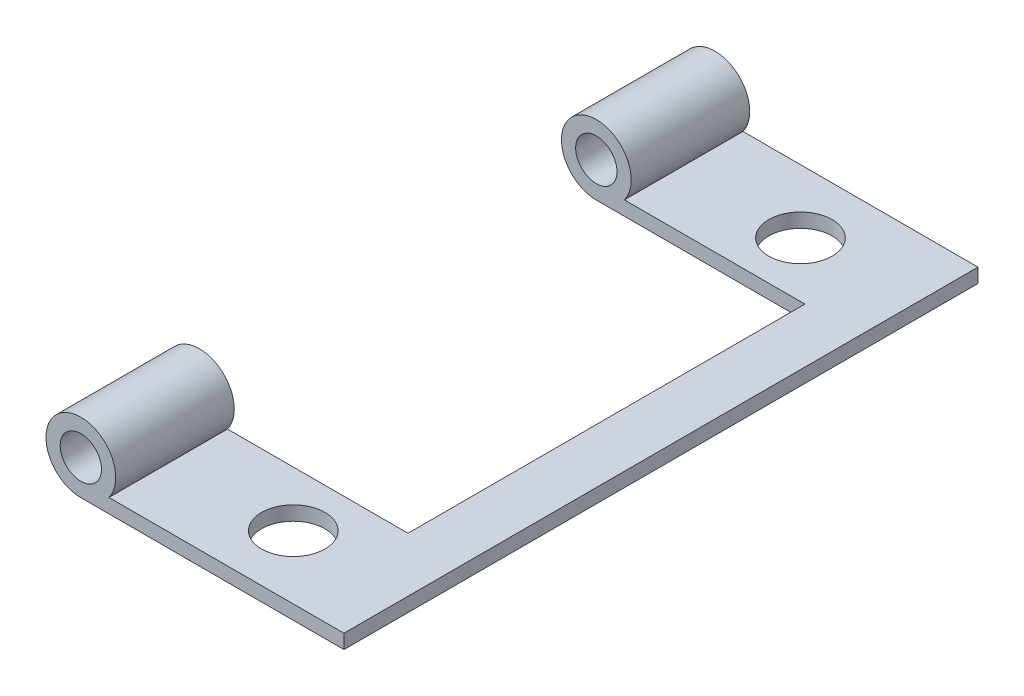
SolidWorks part; units mm, degrees
ref_plane "Front Plane" through (0, 0, 0) normal (0, 0, 1) x (1, 0, 0)
ref_plane "Top Plane" through (0, 0, 0) normal (0, 1, 0) x (1, 0, 0)
ref_plane "Right Plane" through (0, 0, 0) normal (1, 0, 0) x (0, 0, -1)
sketch "Sketch2" plane through (0, 0, 0) normal (0, 1, 0) x (1, 0, 0)
  line L0 (0, 25) -> (0, -25) construction
  line L1 (-9, 25) -> (9, 25)
  line L2 (-9, 25) -> (-9, 15.65)
  line L3 (-9, -25) -> (9, -25)
  line L4 (9, 25) -> (9, -25)
  line L5 (-9, 25) -> (9, -25) construction
  line L6 (-9, -25) -> (9, 25) construction
  line L7 (0, 22.5) -> (9, 22.5) construction
  line L8 (0, -22.5) -> (9, -22.5) construction
  line L9 (-9, -15.65) -> (-9, -25)
  line L10 (-9, 15.65) -> (4.7, 15.65)
  line L12 (-9, -15.65) -> (4.7, -15.65)
  line L13 (4.7, 15.65) -> (4.7, -15.65)
  circle A0 centre (0, 20) radius 2.5
  circle A1 centre (0, -20) radius 2.5
  point P0 (0, 0)
  point P20 (4.7, 0)
  dimension "D3" = 5
  dimension "D1" = 50
  dimension "D2" = 18
  dimension "D4" = 2.5
  dimension "D5" = 2.5
  dimension "D6" = 31.3
  dimension "D7" = 13.7
extrude "Boss-Extrude1" add sketch "Sketch2" along normal blind 1.12
sketch "Sketch3" plane through (0, 0, -25) normal (0, 0, -1) x (-1, 0, 0)
  line L1 (9, 1.12) -> (9, 0) construction
  line L2 (-9, 0) -> (9, 0) construction
  line L4 (9, 1.12) -> (9.5351, 1.12)
  line L5 (9, 1.12) -> (9, 0)
  line L6 (9, 0) -> (11.75, 0)
  arc A0 (11.75, 0) -> (9.5351, 1.12) centre (11.75, 2.75) ccw
  circle A1 centre (11.75, 2.75) radius 1.63
  dimension "D1" = 5.5
  dimension "D2" = 3.26
extrude "Boss-Extrude2" add sketch "Sketch3" against normal up to surface (40.65 mm away)
mirror "Mirror2" about plane through (0, 0, 0) normal (0, 0, 1) of "Boss-Extrude2"
sketch "Sketch4" plane through (0, 1.12, 0) normal (0, 1, 0) x (1, 0, 0)
  line L0 (-9, 15.65) -> (4.7, 15.65) construction
  line L1 (4.7, -15.65) -> (-14.5, -15.65)
  line L2 (4.7, -15.65) -> (4.7, 15.65)
  line L3 (4.7, 15.65) -> (-14.5, 15.65)
  line L4 (-14.5, -15.65) -> (-14.5, 15.65)
  line L5 (4.7, -15.65) -> (-9, -15.65) construction
  line L6 (-14.5, 25) -> (-14.5, -25) construction
extrude "Cut-Extrude2" cut sketch "Sketch4" along normal through all both and the other way through all
